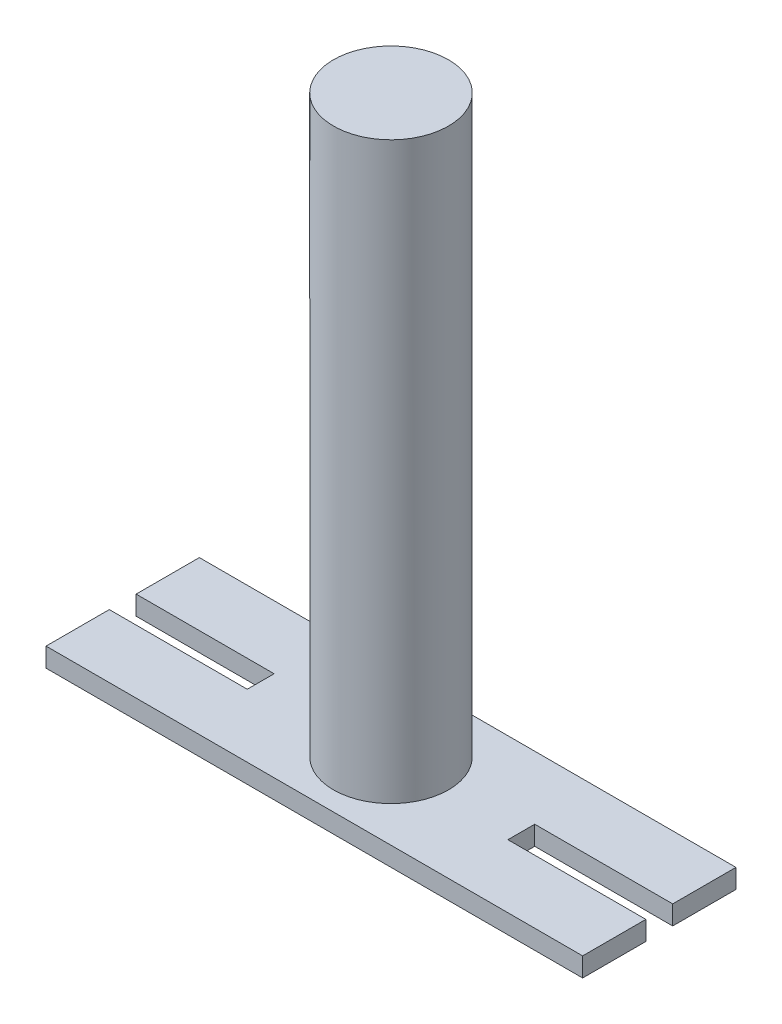
SolidWorks part; units mm, degrees
ref_plane "Front Plane" through (0, 0, 0) normal (0, 0, 1) x (1, 0, 0)
ref_plane "Top Plane" through (0, 0, 0) normal (0, 1, 0) x (1, 0, 0)
ref_plane "Right Plane" through (0, 0, 0) normal (1, 0, 0) x (0, 0, -1)
sketch "Sketch2" plane through (0, 0, 0) normal (0, 1, 0) x (1, 0, 0)
  line L0 (0, 508) -> (0, -508) construction
  line L1 (1778, 508) -> (-1778, 508)
  line L2 (1778, 508) -> (1778, 88.9)
  line L3 (1778, -508) -> (-1778, -508)
  line L4 (-1778, 508) -> (-1778, 88.9)
  line L5 (1778, 508) -> (-1778, -508) construction
  line L6 (1778, -508) -> (-1778, 508) construction
  line L7 (-1778, -88.9) -> (-863.6, -88.9)
  line L8 (-863.6, -88.9) -> (-863.6, 88.9)
  line L9 (-863.6, 0) -> (-1778, 0) construction
  line L10 (-1778, 88.9) -> (-863.6, 88.9)
  line L11 (1778, 88.9) -> (863.6, 88.9)
  line L12 (863.6, -88.9) -> (863.6, 88.9)
  line L13 (1778, -88.9) -> (863.6, -88.9)
  line L14 (-1778, -88.9) -> (-1778, -508)
  line L15 (1778, -88.9) -> (1778, -508)
  circle A0 centre (0, 0) radius 254
  point P0 (0, 0)
  dimension "D3" = 508
  dimension "D1" = 3556
  dimension "D2" = 1016
  dimension "D4" = 419.1
  dimension "D5" = 914.4
extrude "Boss-Extrude1" add sketch "Sketch2" along normal blind 127 contours L15 L13 L12 L11 L2 L1 L4 L10 L8 L7 L14 L3 A0 | A0
sketch "Sketch3" plane through (0, 0, 0) normal (0, 0, 1) x (1, 0, 0)
  line L0 (0, 0) -> (0, 3937) construction
  line L1 (1778, 0) -> (-1778, 0) construction
  line L2 (0, 3937) -> (381, 3937)
  line L3 (381, 3937) -> (381, 127)
  line L4 (1778, 127) -> (-1778, 127) construction
  line L5 (381, 127) -> (254, 127)
  line L6 (254, 127) -> (254, 3810)
  line L7 (254, 3810) -> (0, 3810)
  line L8 (254, 0) -> (254, 127) construction
  line L9 (0, 3937) -> (0, 3810)
  dimension "D1" = 3937
  dimension "D2" = 381
  dimension "D3" = 3683
revolve "Revolve1" add sketch "Sketch3" angle 360 about L0
